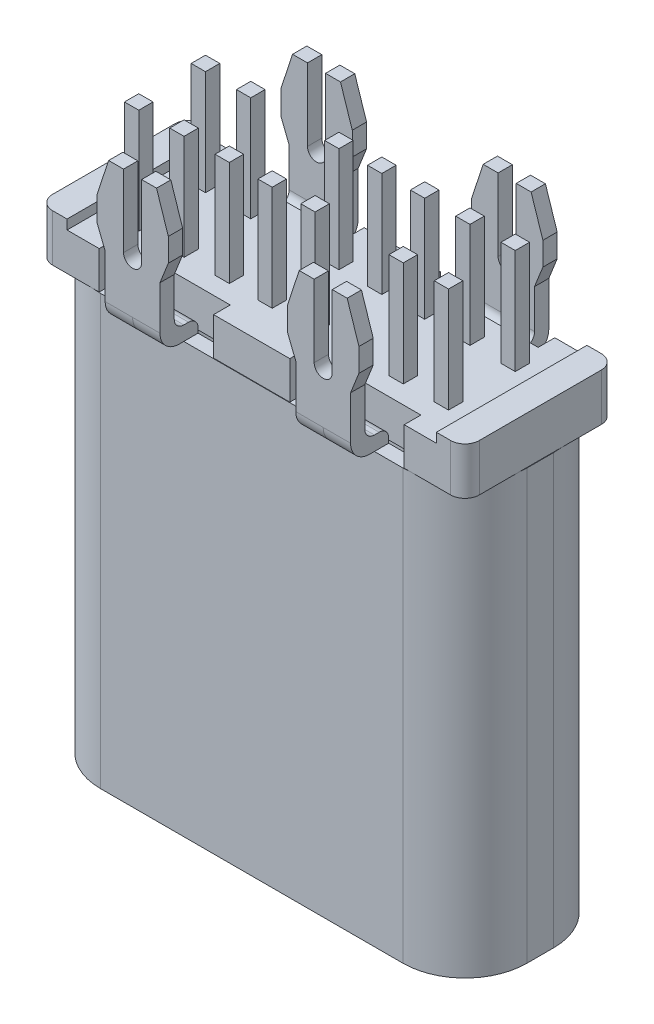
SolidWorks part; units mm, degrees
ref_plane "Front" through (0, 0, 0) normal (0, 0, 1) x (1, 0, 0)
ref_plane "Top" through (0, 0, 0) normal (0, 1, 0) x (1, 0, 0)
ref_plane "Right" through (0, 0, 0) normal (1, 0, 0) x (0, 0, -1)
sketch "草图1" plane through (0, 0, 0) normal (0, 1, 0) x (1, 0, 0)
  line L6 (4.475, -0.28) -> (4.475, 0.28)
  line L7 (3.175, 1.58) -> (-3.175, 1.58)
  line L8 (-4.475, 0.28) -> (-4.475, -0.28)
  line L9 (-3.175, -1.58) -> (3.175, -1.58)
  line L11 (3.175, -1.28) -> (-3.175, -1.28)
  line L12 (-4.175, -0.28) -> (-4.175, 0.28)
  line L13 (-3.175, 1.28) -> (3.175, 1.28)
  line L14 (4.175, 0.28) -> (4.175, -0.28)
  line L16 (-3.175, 1.28) -> (3.175, -1.28) construction
  line L17 (3.175, 1.28) -> (-3.175, -1.28) construction
  line L18 (-3.175, -1.28) -> (3.175, -1.28) construction
  line L19 (4.175, -0.28) -> (4.175, 0.28) construction
  line L20 (3.175, 1.28) -> (-3.175, 1.28) construction
  line L21 (-4.175, 0.28) -> (-4.175, -0.28) construction
  arc A0 (3.175, -1.58) -> (4.475, -0.28) centre (3.175, -0.28) ccw
  arc A1 (4.475, 0.28) -> (3.175, 1.58) centre (3.175, 0.28) ccw
  arc A2 (-3.175, 1.58) -> (-4.475, 0.28) centre (-3.175, 0.28) ccw
  arc A3 (-4.475, -0.28) -> (-3.175, -1.58) centre (-3.175, -0.28) ccw
  arc A4 (-4.175, -0.28) -> (-3.175, -1.28) centre (-3.175, -0.28) ccw
  arc A5 (-3.175, 1.28) -> (-4.175, 0.28) centre (-3.175, 0.28) ccw
  arc A6 (4.175, 0.28) -> (3.175, 1.28) centre (3.175, 0.28) ccw
  arc A7 (3.175, -1.28) -> (4.175, -0.28) centre (3.175, -0.28) ccw
  arc A8 (3.175, -1.28) -> (4.175, -0.28) centre (3.175, -0.28) ccw construction
  arc A9 (4.175, 0.28) -> (3.175, 1.28) centre (3.175, 0.28) ccw construction
  arc A10 (-3.175, 1.28) -> (-4.175, 0.28) centre (-3.175, 0.28) ccw construction
  arc A11 (-4.175, -0.28) -> (-3.175, -1.28) centre (-3.175, -0.28) ccw construction
  point P15 (-4.1564, 0.28)
  point P16 (0, 0)
  point P17 (3.175, 1.3114)
  point P18 (0, 0)
  point P20 (4.1453, 0.28)
  point P36 (-4.1564, -0.28)
  point P37 (-3.175, 1.3071)
  point P38 (4.2078, -0.28)
  dimension "D1" = 0.3
  dimension "D2" = 0.3
extrude "凸台-拉伸1" add sketch "草图1" along normal blind 9
ref_plane "基准面1" through (0, 9.01, 0) normal (0, 1, 0) x (1, 0, 0)
ref_plane "基准面2" through (-2, 0, 0) normal (1, 0, 0) x (0, 0, -1)
sketch "草图4" plane through (-2, 0, 0) normal (1, 0, 0) x (0, 0, -1)
  line L0 (-1.28, 9) -> (-1.28, 9.3)
  line L1 (-1.28, 9.3) -> (-1.78, 9.3)
  line L2 (-1.78, 9.3) -> (-1.78, 12)
  line L3 (-1.78, 12) -> (-2.08, 12)
  line L4 (-2.08, 12) -> (-2.08, 9)
  line L5 (-2.08, 9) -> (-1.28, 9)
  line L6 (-1.58, 7.6761) -> (-1.28, 7.6761) construction
  line L7 (-1.58, 9) -> (-1.58, 0) construction
  line L8 (-1.28, 9) -> (-1.28, 0) construction
  line L9 (0.28, 9) -> (-0.28, 9) construction
  line L10 (0, 9) -> (0, 0) construction
  line L11 (0.28, 0) -> (-0.28, 0) construction
  line L12 (-0.28, 9) -> (-1.58, 9) construction
  point P19 (-1.93, 12)
  dimension "D1" = 1.93
  dimension "D2" = 3
extrude "凸台-拉伸3" add sketch "草图4" along normal blind 0.75
sketch "草图5" plane through (0, 0, 2.08) normal (0, 0, 1) x (1, 0, 0)
  line L0 (0, 0) -> (4.475, 0) construction
  line L1 (-1.25, 9) -> (-1.4256, 9)
  line L2 (-1.25, 9) -> (-2, 9) construction
  line L3 (-1.4256, 9) -> (-1.4256, 10.3167)
  line L4 (-1.4256, 10.3167) -> (-1.25, 10.7582)
  line L5 (-1.25, 12) -> (-1.25, 9) construction
  line L6 (-1.25, 10.7582) -> (-1.25, 11.246)
  line L7 (-1.25, 11.246) -> (-1.4971, 12)
  line L8 (-1.25, 12) -> (-2, 12) construction
  line L9 (-1.4971, 12) -> (-1.8104, 12)
  line L10 (-1.8104, 12) -> (-1.8104, 10.4828)
  line L12 (-2, 12) -> (-2, 9) construction
  line L13 (-2, 10.2931) -> (-2, 12.1906)
  line L14 (-2, 12.1906) -> (-1.0086, 12.1906)
  line L15 (-1.0086, 12.1906) -> (-1.0086, 9)
  line L16 (-1.25, 9) -> (3.175, 9) construction
  line L17 (-1.0086, 9) -> (-1.4256, 9)
  arc A0 (-2, 10.2931) -> (-1.8104, 10.4828) centre (-2, 10.4828) ccw
extrude "切除-拉伸2" cut sketch "草图5" against normal through all
fillet "圆角1" radius 0.2 2 edges at (-1.7128, 9.3, 1.78) (-1.7128, 9.3, 1.28)
fillet "圆角2" radius 0.4 1 edges at (-1.7128, 9, 2.08)
mirror "镜向1" about plane through (-2, 0, 0) normal (1, 0, 0) of "圆角2", "圆角1", "切除-拉伸2", "凸台-拉伸3"
sketch "草图8" plane through (0, 0, 0) normal (0, -1, 0) x (1, 0, 0)
  line L1 (0, 0) -> (-5.472, 0)
  line L2 (0, 0) -> (0, 3.2363)
  line L5 (0, 3.2363) -> (5.6224, 3.2363)
  line L6 (-5.472, 0) -> (-5.472, -3.358)
  line L7 (-5.472, -3.358) -> (5.6224, -3.358)
  line L8 (5.6224, 3.2363) -> (5.6224, -3.358)
extrude "切除-拉伸4" cut sketch "草图8" against normal through all
mirror "镜向6" about plane through (0, 0, 0) normal (0, 0, 1) of bodies 108
sketch "草图2" plane through (0, 9.01, 0) normal (0, 1, 0) x (1, 0, 0)
  line L0 (-4.475, 0.28) -> (-4.475, -0.28) construction
  line L1 (0, -1.58) -> (-0.8, -1.58)
  line L4 (-4.475, -1.58) -> (-4.475, 1.58)
  line L5 (-3.2, 1.58) -> (-4.475, 1.58)
  line L6 (0, 0) -> (-4.475, -1.58) construction
  line L8 (-2, -1.68) -> (-2, 0.1023) construction
  line L9 (-2, -1.78) -> (-2, -1.58) construction
  line L10 (-3.2, -1.58) -> (-4.475, -1.58)
  line L11 (-3.2, -1.23) -> (-0.8, -1.23)
  line L12 (-3.2, -1.23) -> (-3.2, -1.58)
  line L14 (-0.8, -1.23) -> (-0.8, -1.58)
  line L15 (-3.2, -1.23) -> (-0.8, -1.58) construction
  line L16 (-3.2, -1.58) -> (-0.8, -1.23) construction
  line L19 (0, 1.58) -> (0, -1.58)
  line L20 (-4.475, 0) -> (0, 0) construction
  line L21 (-3.2, 1.23) -> (-3.2, 1.58)
  line L22 (-3.2, 1.23) -> (-0.8, 1.23)
  line L23 (-0.8, 1.23) -> (-0.8, 1.58)
  line L24 (0, 1.58) -> (-0.8, 1.58)
  point P0 (0, 0)
  point P14 (-2, -1.405)
  dimension "D1" = 0.35
  dimension "D2" = 2.4
extrude "凸台-拉伸2" add sketch "草图2" along normal blind 0.99
sketch "草图6" plane through (0, 10, 0) normal (0, 1, 0) x (1, 0, 0)
  line L0 (-0.8, -1.58) -> (0, -1.58) construction
  line L1 (-3.875, 1.58) -> (3.875, 1.58)
  line L2 (-3.875, 1.58) -> (-3.875, -1.58)
  line L3 (-3.875, -1.58) -> (3.875, -1.58)
  line L4 (3.875, 1.58) -> (3.875, -1.58)
  line L5 (-3.875, 1.58) -> (3.875, -1.58) construction
  line L6 (-3.875, -1.58) -> (3.875, 1.58) construction
  line L7 (-4.475, 1.58) -> (-4.475, -1.58) construction
  point P0 (0, 0)
  dimension "D1" = 0.6
extrude "切除-拉伸3" cut sketch "草图6" against normal blind 0.2
fillet "圆角3" radius 0.3 2 edges at (-4.475, 9.505, 1.58) (-4.475, 9.505, -1.58)
sketch "草图7" plane through (0, 9.8, 0) normal (0, 1, 0) x (1, 0, 0)
  line L0 (-2.15, -0.55) -> (-2.15, -0.85)
  line L1 (-3.4, -0.55) -> (-3.1, -0.55)
  line L2 (-3.4, -0.55) -> (-3.4, -0.85)
  line L3 (-3.4, -0.85) -> (-3.1, -0.85)
  line L4 (-3.1, -0.55) -> (-3.1, -0.85)
  line L5 (-3.4, -0.55) -> (-3.1, -0.85) construction
  line L6 (-3.4, -0.85) -> (-3.1, -0.55) construction
  line L7 (-2.45, -0.85) -> (-2.15, -0.85)
  line L8 (-2.45, -0.55) -> (-2.45, -0.85)
  line L9 (-2.45, -0.55) -> (-2.15, -0.55)
  line L18 (-2.15, 0.85) -> (-2.15, 0.55)
  line L19 (-2.45, 0.55) -> (-2.15, 0.55)
  line L20 (-2.45, 0.85) -> (-2.45, 0.55)
  line L21 (-2.45, 0.85) -> (-2.15, 0.85)
  line L30 (-3.1, 0.85) -> (-3.1, 0.55)
  line L31 (-3.4, 0.55) -> (-3.1, 0.55)
  line L32 (-3.4, 0.85) -> (-3.4, 0.55)
  line L33 (-3.4, 0.85) -> (-3.1, 0.85)
  line L34 (-3.1, -0.55) -> (-2.15, -0.55) construction
  line L35 (-3.1, -0.55) -> (-3.1, 0.85) construction
  line L36 (-3.25, -0.7) -> (0, -0.7) construction
  line L37 (0, -0.7) -> (0, 0) construction
  line L38 (-0.6, -0.85) -> (-0.3, -0.85)
  line L39 (-1.5, -0.55) -> (-1.2, -0.55)
  line L40 (-1.5, -0.55) -> (-1.5, -0.85)
  line L41 (-1.5, -0.85) -> (-1.2, -0.85)
  line L42 (-1.2, -0.55) -> (-1.2, -0.85)
  line L43 (-1.5, -0.55) -> (-1.2, -0.85) construction
  line L44 (-1.5, -0.85) -> (-1.2, -0.55) construction
  line L45 (-0.3, -0.55) -> (-0.3, -0.85)
  line L46 (-0.6, -0.55) -> (-0.3, -0.55)
  line L47 (-0.6, -0.55) -> (-0.6, -0.85)
  line L48 (-0.6, 0.55) -> (-0.3, 0.55)
  line L49 (-0.3, 0.85) -> (-0.3, 0.55)
  line L50 (-0.6, 0.85) -> (-0.3, 0.85)
  line L51 (-0.6, 0.85) -> (-0.6, 0.55)
  line L52 (-1.5, 0.55) -> (-1.2, 0.55)
  line L53 (-1.2, 0.85) -> (-1.2, 0.55)
  line L54 (-1.5, 0.85) -> (-1.2, 0.85)
  line L55 (-1.5, 0.85) -> (-1.5, 0.55)
  line L56 (-1.5, -0.85) -> (-0.6, -0.85) construction
  line L57 (-1.5, -0.85) -> (-1.5, 0.55) construction
  point P0 (-3.25, -0.7)
  point P13 (-1.35, -0.7)
  dimension "D1" = 0.3
  dimension "D2" = 45
  dimension "D3" = 3.25
  dimension "D4" = 0.7
  dimension "D7" = 0.95
  dimension "D8" = 1.4
  dimension "D9" = 1.35
  dimension "D12" = 0.9
  dimension "D13" = 1.4
  dimension "D5" = 2
  dimension "D6" = 2
  dimension "D10" = 2
  dimension "D11" = 2
extrude "凸台-拉伸4" add sketch "草图7" along normal blind 2.2 contours L46 L47 L38 L45 | L50 L51 L48 L49 | L9 L8 L7 L0 | L21 L20 L19 L18 | L33 L32 L31 L30 | L42 L39 L40 L41 | L4 L1 L2 L3 | L52 L53 L54 L55
mirror "镜向9" about plane through (0, 12, 0) normal (-1, 0, 0) of bodies 109 107
sketch "草图10" plane through (0, 12, 0) normal (0, 1, 0) x (1, 0, 0)
  line L4 (-1.5, 0.85) -> (-1.5, 0.55)
  line L5 (-1.5, 0.55) -> (-1.2, 0.55)
  line L6 (-1.2, 0.55) -> (-1.2, 0.85)
  line L7 (-1.2, 0.85) -> (-1.5, 0.85)
  line L8 (-1.5, 0.85) -> (-1.5, 0.55)
  line L9 (-1.5, 0.55) -> (-1.2, 0.55)
  line L10 (-1.2, 0.55) -> (-1.2, 0.85)
  line L11 (-1.2, 0.85) -> (-1.5, 0.85)
  line L12 (1.2, -0.55) -> (1.2, -0.85)
  line L13 (1.2, -0.85) -> (1.5, -0.85)
  line L14 (1.5, -0.85) -> (1.5, -0.55)
  line L15 (1.5, -0.55) -> (1.2, -0.55)
  line L16 (1.2, -0.55) -> (1.2, -0.85)
  line L17 (1.2, -0.85) -> (1.5, -0.85)
  line L18 (1.5, -0.85) -> (1.5, -0.55)
  line L19 (1.5, -0.55) -> (1.2, -0.55)
  dimension "D1" = 0
  dimension "D2" = 0
extrude "切除-拉伸6" cut sketch "草图10" against normal up to surface (2.2 mm away) up to face at (-3.25, 9.8, 0.7)
ref_plane "基准面3" through (0, 0, 0) normal (1, 0, 0) x (0, 0, -1)
ref_plane "基准面4" through (0, 0, 0) normal (0, 0, -1) x (-1, 0, 0)
chamfer "倒角1" distance 0.1 angle 45 8 edges at (-4.175, 0, 0) (-3.8821, 0, 0.9871) (0, 0, 1.28) (-3.8821, 0, -0.9871) (0, 0, -1.28) (3.8821, 0, -0.9871) (4.175, 0, 0) (3.8821, 0, 0.9871)
